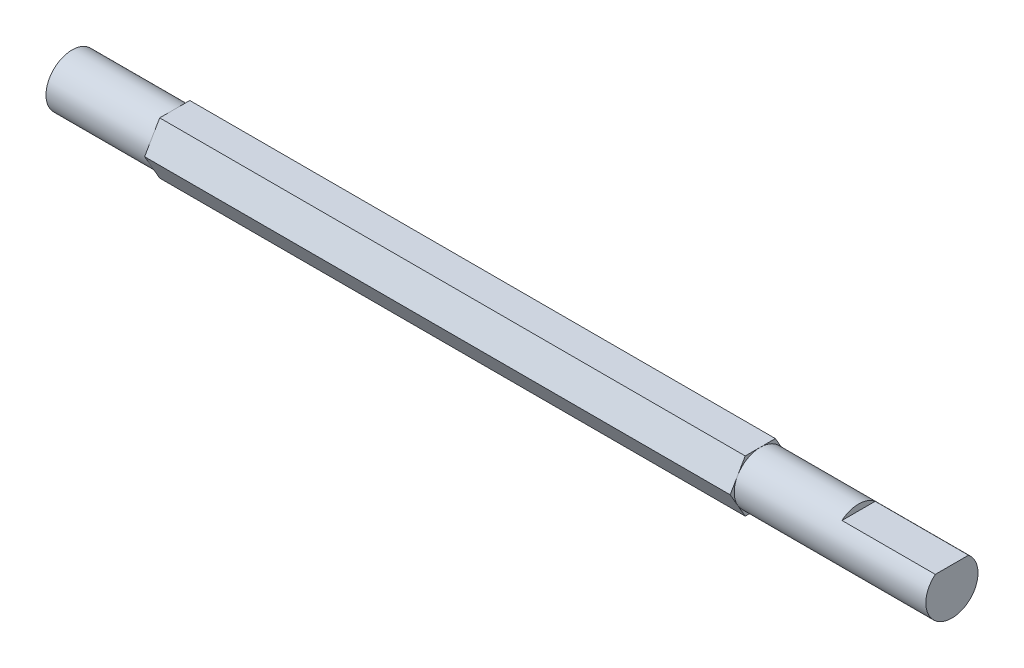
SolidWorks part; units mm, degrees
ref_plane "Ebene vorne" through (0, 0, 0) normal (0, 0, 1) x (1, 0, 0)
ref_plane "Ebene oben" through (0, 0, 0) normal (0, 1, 0) x (1, 0, 0)
ref_plane "Ebene rechts" through (0, 0, 0) normal (1, 0, 0) x (0, 0, -1)
sketch "Skizze1" plane through (0, 0, 0) normal (1, 0, 0) x (0, 0, -1)
  circle A0 centre (0, 0) radius 2.795
  dimension "D1" = 5.59
extrude "Aufsatz-Linear austragen1" add sketch "Skizze1" along normal blind 94.27 contours A0
ref_plane "Ebene1" through (11, 0, 0) normal (1, 0, 0) x (0, 0, -1)
sketch "Skizze2" plane through (11, 0, 0) normal (1, 0, 0) x (0, 0, -1)
  line L0 (1.6137, 2.795) -> (-1.6137, 2.795)
  line L1 (-1.6137, 2.795) -> (-3.2274, 0)
  line L2 (1.6137, -2.795) -> (-1.6137, -2.795)
  line L3 (-1.6137, -2.795) -> (-3.2274, 0)
  line L4 (1.6137, 2.795) -> (3.2274, 0)
  line L5 (1.6137, -2.795) -> (3.2274, 0)
  line L6 (-3.565, 0) -> (3.1629, 0)
  circle A0 centre (0, 0) radius 2.795 construction
  dimension "D4" = 5.59
  dimension "D1" = 120
  dimension "D2" = 120
  dimension "D3" = 120
  dimension "D5" = 120
extrude "Aufsatz-Linear austragen2" add sketch "Skizze2" along normal blind 62.74
sketch "Skizze3" plane through (0, 0, 0) normal (1, 0, 0) x (0, 0, -1)
  line L0 (0, 2.155) -> (0, -2.795) construction
  line L1 (1.7799, 2.155) -> (-1.7799, 2.155)
  circle A0 centre (0, 0) radius 2.795 construction
  arc A1 (1.7799, 2.155) -> (-1.7799, 2.155) centre (0, 0) ccw
  dimension "D1" = 4.95
extrude "Schnitt-Linear austragen1" cut sketch "Skizze3" against normal blind 10 from surface at 94.27 starting at face at (94.27, 0, -2.795)
